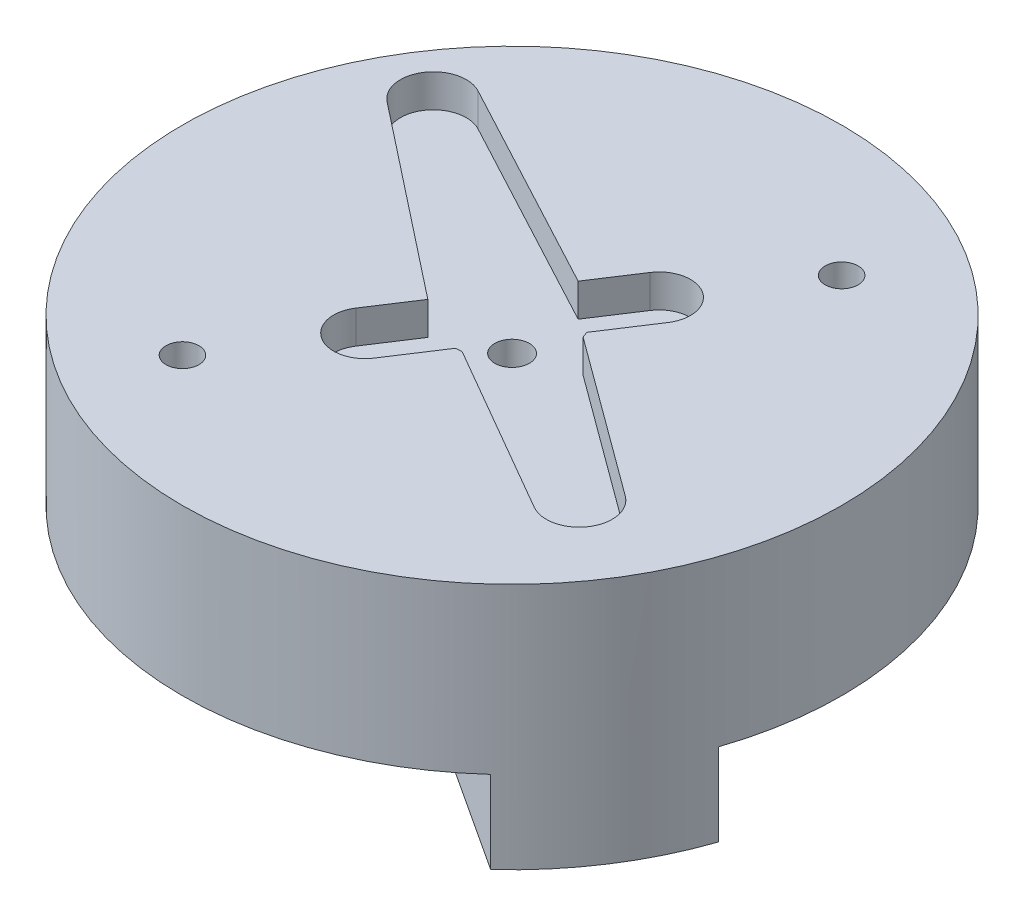
SolidWorks part; units mm, degrees
material "PVC Rigid"
ref_plane "Front Plane" through (0, 0, 0) normal (0, 0, 1) x (1, 0, 0)
ref_plane "Top Plane" through (0, 0, 0) normal (0, 1, 0) x (1, 0, 0)
ref_plane "Right Plane" through (0, 0, 0) normal (1, 0, 0) x (0, 0, -1)
sketch "Sketch1" plane through (0, 0, 0) normal (0, 1, 0) x (1, 0, 0)
  line L0 (-39.7574, 0.1279) -> (-13.554, -16.9915) construction
  line L1 (-33.5544, -21.1852) -> (-17.7477, 3.009) construction
  line L2 (-22.3523, -8.0779) -> (-12.7052, -15.1605)
  line L3 (-25.4393, -5.2902) -> (-38.4804, 1.6734)
  line L4 (-40.6597, -1.6623) -> (-29.0441, -10.8077)
  line L5 (-29.0441, -10.8077) -> (-30.7695, -13.4487)
  line L6 (-27.5882, -15.527) -> (-25.6355, -12.5381)
  line L7 (-25.6355, -12.5381) -> (-25.2511, -12.5149)
  line L8 (-25.2511, -12.5149) -> (-14.8897, -18.5042)
  line L10 (-22.3523, -8.0779) -> (-22.4854, -7.7165)
  line L11 (-22.4854, -7.7165) -> (-20.5326, -4.7276)
  line L12 (-23.7139, -2.6492) -> (-25.4393, -5.2902)
  arc A5 (-38.4804, 1.6734) -> (-40.6597, -1.6623) centre (-39.4225, -0.0909) ccw
  arc A6 (-30.7695, -13.4487) -> (-27.5882, -15.527) centre (-29.1788, -14.4879) ccw
  arc A7 (-14.8897, -18.5042) -> (-12.7052, -15.1605) centre (-13.8888, -16.7727) ccw
  arc A8 (-20.5326, -4.7276) -> (-23.7139, -2.6492) centre (-22.1233, -3.6884) ccw
  circle A9 centre (-25.6511, -9.0881) radius 20
  circle A10 centre (-25.6511, -9.0881) radius 3
  circle A11 centre (-33.5544, -21.1852) radius 1
  circle A12 centre (-17.7477, 3.009) radius 1
  circle A13 centre (-25.6511, -9.0881) radius 14.45 construction
  point P46 (-39.7574, 0.1279)
extrude "Boss-Extrude1" add sketch "Sketch1" along normal blind 2 separate body contours A9 A8 L11 L10 L2 A7 L8 L7 L6 A6 L5 L4 A5 L3 L12 A12 A11
sketch "Sketch2" plane through (0, 0, 0) normal (0, -1, 0) x (1, 0, 0)
  line L0 (-33.5544, 21.1852) -> (-17.7477, -3.009) construction
  circle A4 centre (-17.7477, -3.009) radius 1
  circle A5 centre (-33.5544, 21.1852) radius 1
  circle A6 centre (-25.6511, 9.0881) radius 2.3
  circle A7 centre (-25.6511, 9.0881) radius 20
extrude "Boss-Extrude3" add sketch "Sketch2" along normal blind 8
sketch "Sketch3" plane through (0, -8, 0) normal (0, -1, 0) x (1, 0, 0)
  line L0 (-33.5544, 21.1852) -> (-17.7477, -3.009) construction
  line L1 (-25.6511, 9.0881) -> (-23.7256, 10.3461) construction
  line L2 (-23.7256, 10.3461) -> (-26.4603, 14.5319)
  line L9 (-23.7256, 10.3461) -> (-20.9908, 6.1602)
  line L10 (-26.4603, 14.5319) -> (-12.1741, 23.8655)
  line L11 (-20.9908, 6.1602) -> (-6.7046, 15.4938)
  line L12 (-27.5765, 7.8301) -> (-24.8418, 3.6443)
  line L13 (-24.8418, 3.6443) -> (-39.128, -5.6893)
  line L14 (-30.3113, 12.016) -> (-44.5975, 2.6824)
  line L15 (-27.5765, 7.8301) -> (-30.3113, 12.016)
  arc A0 (-39.128, -5.6893) -> (-44.5975, 2.6824) centre (-25.6511, 9.0881) cw
  circle A3 centre (-25.6511, 9.0881) radius 2.3 construction
  circle A4 centre (-25.6511, 9.0881) radius 20 construction
  arc A5 (-6.7046, 15.4938) -> (-12.1741, 23.8655) centre (-25.6511, 9.0881) ccw
  dimension "D1" = 90
  dimension "D2" = 5
  dimension "D3" = 5
extrude "Boss-Extrude4" add sketch "Sketch3" along normal blind 5
sketch "Sketch4" plane through (0, 0, 0) normal (0, 1, 0) x (1, 0, 0)
  circle A0 centre (-25.6511, -9.0881) radius 2.3
  circle A1 centre (-25.6511, -9.0881) radius 1.05
  dimension "D1" = 2.1
extrude "Boss-Extrude5" add sketch "Sketch4" against normal blind 2
sketch "Sketch5" plane through (0, 2, 0) normal (0, 1, 0) x (1, 0, 0)
  circle A0 centre (-20.1275, 54.7732) radius 0.7401
extrude "Cut-Extrude1" cut sketch "Sketch5" against normal blind 6
